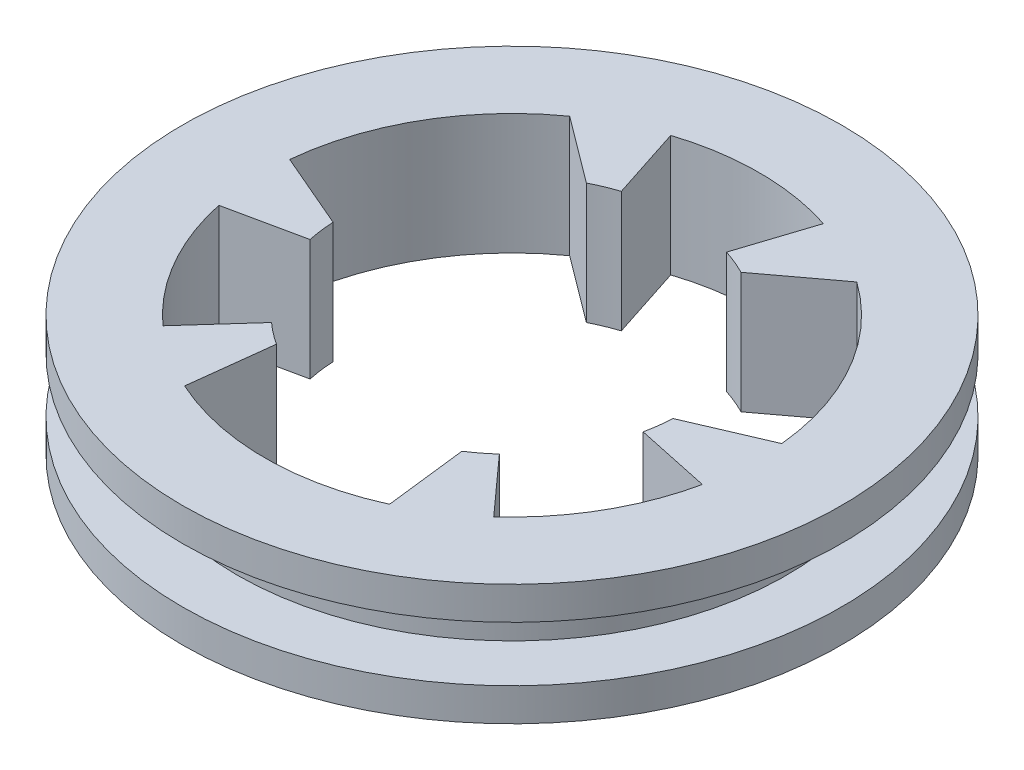
SolidWorks part; units mm, degrees
material "AISI Type 316L stainless steel"
ref_plane "Front Plane" through (0, 0, 0) normal (0, 0, 1) x (1, 0, 0)
ref_plane "Top Plane" through (0, 0, 0) normal (0, 1, 0) x (1, 0, 0)
ref_plane "Right Plane" through (0, 0, 0) normal (1, 0, 0) x (0, 0, -1)
sketch "Sketch2" plane through (0, 0, 0) normal (0, 0, 1) x (1, 0, 0)
  line L0 (0, 19.9874) -> (0, -21.8183) construction
  line L1 (0, -55) -> (0, 55) construction
  line L2 (-25, 2.5) -> (-25, -2.5)
  line L3 (55, 0) -> (-55, 0) construction
  line L4 (-25, 2.5) -> (-30, 2.5)
  line L5 (-30, 2.5) -> (-30, 5.5)
  line L6 (-30, 5.5) -> (0, 5.5)
  line L7 (-25, -2.5) -> (-30, -2.5)
  line L8 (-30, -2.5) -> (-30, -5.5)
  line L9 (-30, -5.5) -> (0, -5.5)
  line L10 (0, 5.5) -> (0, -5.5)
  point P7 (-25, 0)
  dimension "D1" = 5
  dimension "D2" = 5
  dimension "D3" = 3
  dimension "D4" = 3
  dimension "D5" = 25
revolve "Revolve1" add sketch "Sketch2" angle 360 about L0
sketch "Sketch3" plane through (0, 5.5, 0) normal (0, 1, 0) x (1, 0, 0)
  line L0 (0, 0) -> (30.2715, -17.4772) construction
  line L1 (0, -6.05) -> (0, 6.05) construction
  line L2 (22.0083, -4.678) -> (15.1613, -3.2226)
  line L3 (15.0554, -16.7208) -> (10.3715, -11.5187)
  line L4 (-22.0083, -4.678) -> (-15.1613, -3.2226)
  line L5 (-15.0554, -16.7208) -> (-10.3715, -11.5187)
  line L6 (6.9529, 21.3988) -> (4.7898, 14.7414)
  line L7 (-6.9529, 21.3988) -> (-4.7898, 14.7414)
  line L8 (-15.4788, -0.8101) -> (-22.396, 2.1609)
  line L9 (-8.441, -13) -> (-9.3266, -20.4759)
  line L10 (-7.0378, 13.8101) -> (-13.0694, 18.3151)
  line L11 (7.0378, 13.8101) -> (13.0694, 18.3151)
  line L12 (15.4788, -0.8101) -> (22.396, 2.1609)
  line L13 (8.441, -13) -> (9.3266, -20.4759)
  circle A0 centre (0, 0) radius 22.5
  circle A1 centre (0, 0) radius 15.5
  circle A2 centre (0, -14) radius 8.5
  circle A3 centre (-12.1244, 7) radius 8.5
  circle A4 centre (12.1244, 7) radius 8.5
  point P15 (0, 0)
  point P28 (0, 0)
  point P42 (0, 0)
  dimension "D1" = 45
  dimension "D2" = 31
  dimension "D4" = 3
  dimension "D3" = 60
  dimension "D5" = 14
  dimension "D7" = 36
  dimension "D6" = 3
  dimension "D8" = 3
extrude "Cut-Extrude1" cut sketch "Sketch3" against normal up to next
